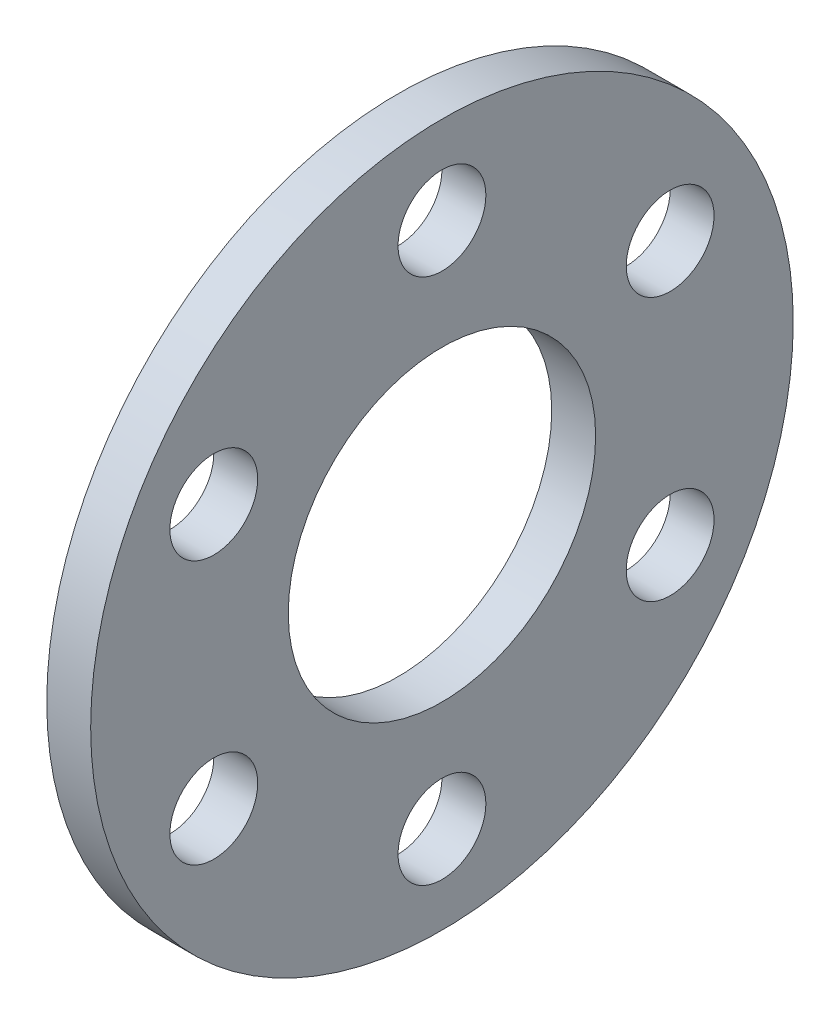
SolidWorks part; units mm, degrees
ref_plane "前视基准面" through (0, 0, 0) normal (0, 0, 1) x (1, 0, 0)
ref_plane "上视基准面" through (0, 0, 0) normal (0, 1, 0) x (1, 0, 0)
ref_plane "右视基准面" through (0, 0, 0) normal (1, 0, 0) x (0, 0, -1)
other "Configuration Table"
sketch "草图1" plane through (0, 0, 0) normal (1, 0, 0) x (0, 0, -1)
  line L0 (0, 0) -> (0, 24) construction
  line L1 (0, 0) -> (-20.7846, 12) construction
  circle A0 centre (0, 0) radius 24
  circle A1 centre (0, 0) radius 10.5
  circle A2 centre (0, 0) radius 18 construction
  circle A3 centre (-15.5885, 9) radius 3
  circle A4 centre (0, 18) radius 3
  circle A5 centre (15.5885, 9) radius 3
  circle A6 centre (15.5885, -9) radius 3
  circle A7 centre (0, -18) radius 3
  circle A8 centre (-15.5885, -9) radius 3
  point P22 (0, 0)
  dimension "D1" = 48
  dimension "D2" = 21
  dimension "D3" = 60
  dimension "D4" = 6
  dimension "D5" = 6
extrude "凸台-拉伸1" add sketch "草图1" along normal blind 3
